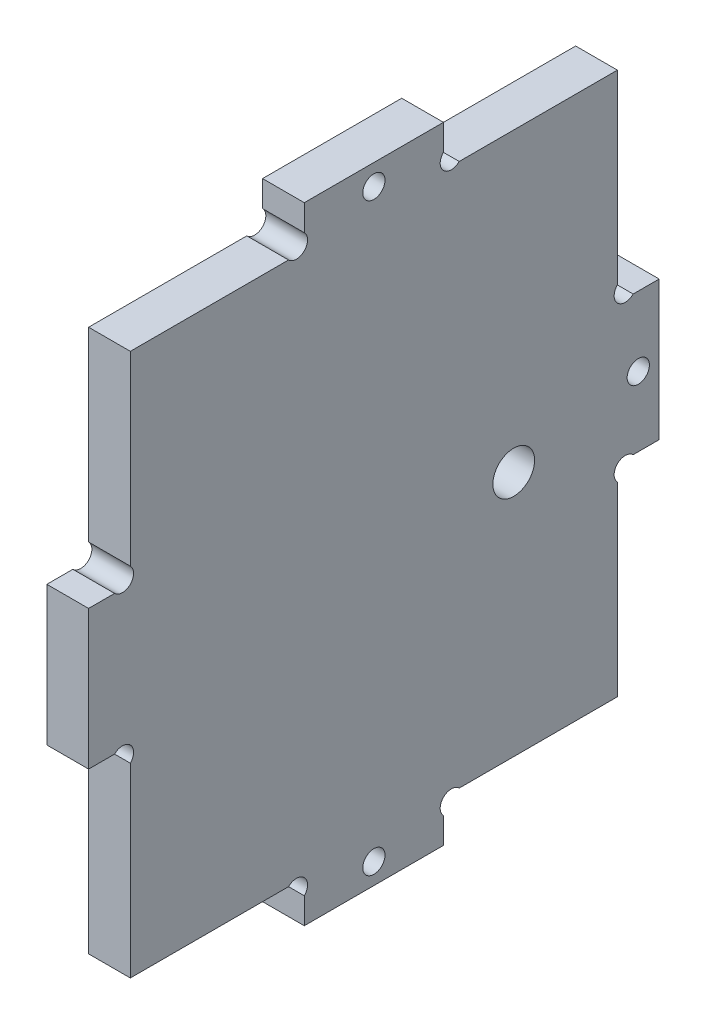
SolidWorks part; units mm, degrees
ref_plane "Plan de face" through (0, 0, 0) normal (0, 0, 1) x (1, 0, 0)
ref_plane "Plan de dessus" through (0, 0, 0) normal (0, 1, 0) x (1, 0, 0)
ref_plane "Plan de droite" through (0, 0, 0) normal (1, 0, 0) x (0, 0, -1)
sketch "Esquisse1" plane through (0, 0, 0) normal (1, 0, 0) x (0, 0, -1)
  line L0 (-35.7035, 0) -> (106.5328, 0) construction
  line L1 (0, -26.8775) -> (0, 120.1432) construction
  line L2 (-35.7035, 90) -> (106.5328, 90) construction
  line L3 (82, -26.8775) -> (82, 120.1432) construction
  line L4 (-26.1182, 45) -> (50.3685, 45) construction
  line L5 (41, 110.1666) -> (41, -12.9771) construction
  line L6 (6, 98.6769) -> (6, -26.8775) construction
  line L7 (-10.2161, 6) -> (106.5328, 6) construction
  line L8 (-13.4887, 35) -> (16.1573, 35) construction
  line L9 (31, 98.6769) -> (31, -12.9771) construction
  line L10 (66.6, 3) -> (33.868, 3) construction
  line L11 (3, 26.4868) -> (3, 50.1651) construction
  line L12 (31, 6) -> (15.8649, -9.1351) construction
  line L13 (6, 32.7373) -> (6, 6)
  line L14 (6, 35) -> (-9.6274, 19.3726) construction
  line L15 (6, 6) -> (28.7373, 6)
  line L16 (31, 3.7373) -> (31, 0)
  line L17 (31, 0) -> (51, 0)
  line L18 (51, 0) -> (51, 3.7373)
  line L19 (3.7373, 35) -> (0, 35)
  line L20 (0, 35) -> (0, 55)
  line L21 (0, 55) -> (3.7373, 55)
  line L22 (53.2627, 6) -> (76, 6)
  line L23 (53.2627, 84) -> (76, 84)
  line L24 (51, 90) -> (51, 86.2627)
  line L25 (6, 84) -> (6, 57.2627)
  line L26 (76, 84) -> (76, 57.2627)
  line L27 (82, 55) -> (78.2627, 55)
  line L28 (82, 35) -> (82, 55)
  line L29 (78.2627, 35) -> (82, 35)
  line L30 (76, 32.7373) -> (76, 6)
  line L31 (31, 90) -> (51, 90)
  line L32 (31, 86.2627) -> (31, 90)
  line L33 (6, 84) -> (28.7373, 84)
  line L35 (92.7604, 41.4) -> (44.1341, 41.4) construction
  line L36 (61.1, -3.0687) -> (61.1, 53.1193) construction
  circle A1 centre (41, 3) radius 1.6
  arc A2 (31, 3.7373) -> (28.7373, 6) centre (29.8686, 4.8686) ccw
  arc A3 (6, 32.7373) -> (3.7373, 35) centre (4.8686, 33.8686) ccw
  arc A4 (51, 3.7373) -> (53.2627, 6) centre (52.1314, 4.8686) cw
  arc A5 (6, 57.2627) -> (3.7373, 55) centre (4.8686, 56.1314) cw
  arc A6 (76, 57.2627) -> (78.2627, 55) centre (77.1314, 56.1314) ccw
  arc A7 (76, 32.7373) -> (78.2627, 35) centre (77.1314, 33.8686) cw
  circle A8 centre (79, 45) radius 1.6
  arc A9 (51, 86.2627) -> (53.2627, 84) centre (52.1314, 85.1314) ccw
  arc A10 (31, 86.2627) -> (28.7373, 84) centre (29.8686, 85.1314) cw
  circle A11 centre (41, 87) radius 1.6
  circle A13 centre (61.1, 41.4) radius 3
  dimension "D13" = 35.4
  dimension "D14" = 20.9
  dimension "D1" = 90
  dimension "D2" = 82
  dimension "D3" = 45
  dimension "D4" = 41
  dimension "D5" = 6
  dimension "D6" = 6
  dimension "D7" = 3
  dimension "D8" = 10
  dimension "D9" = 3
  dimension "D10" = 10
  dimension "D11" = 45
  dimension "D12" = 45
extrude "Boss.-Extru.1" add sketch "Esquisse1" along normal blind 6
